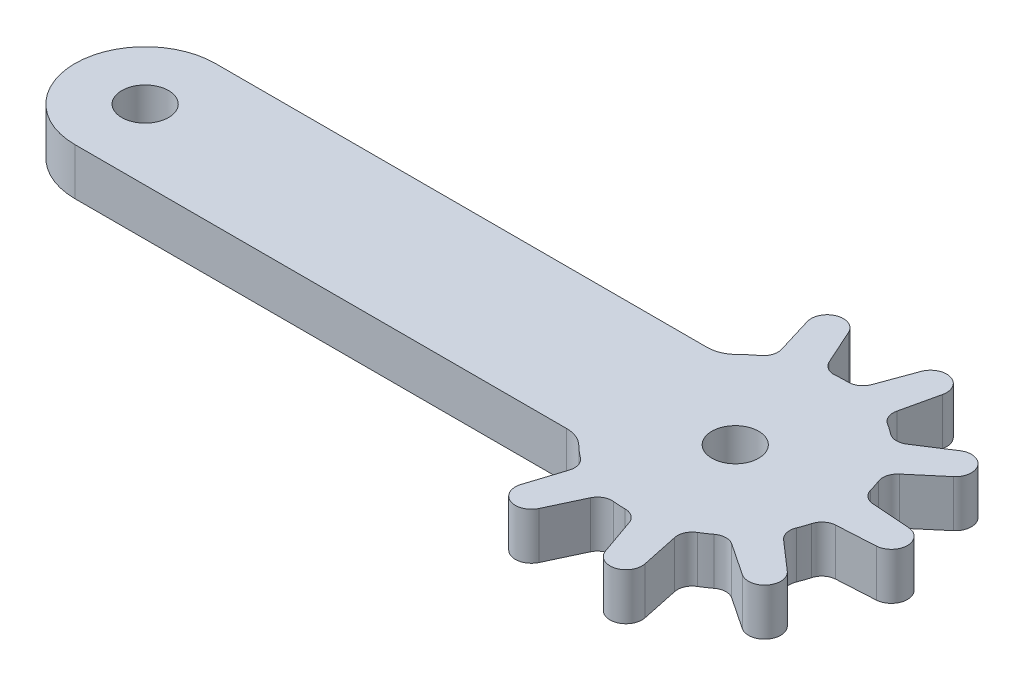
SolidWorks part; units mm, degrees
ref_plane "Alzado" through (0, 0, 0) normal (0, 0, 1) x (1, 0, 0)
ref_plane "Planta" through (0, 0, 0) normal (0, 1, 0) x (1, 0, 0)
ref_plane "Vista lateral" through (0, 0, 0) normal (1, 0, 0) x (0, 0, -1)
sketch "Croquis1" plane through (0, 0, 0) normal (0, 1, 0) x (1, 0, 0)
  line L1 (-20, 0) -> (20, 0)
  line L3 (-20, -9.525) -> (20, -9.525)
  arc A0 (-20, 0) -> (-20, -9.525) centre (-20, -4.7625) ccw
  arc A1 (20, -9.525) -> (20, 0) centre (20, -4.7625) ccw
  circle A2 centre (-20, -4.7625) radius 1.5875
  circle A3 centre (20, -4.7625) radius 1.5875
  dimension "D3" = 4.7625
  dimension "D5" = 3.175
  dimension "D6" = 3.175
  dimension "D1" = 40
  dimension "D2" = 9.525
  dimension "D4" = 40
extrude "Saliente-Extruir1" add sketch "Croquis1" along normal blind 3.175
sketch "Croquis2" plane through (0, 3.175, 0) normal (0, 1, 0) x (1, 0, 0)
  line L0 (20, -1004.7625) -> (20, 48995.2375) construction
  circle A0 centre (20, -4.7625) radius 7.5
  circle A1 centre (20, 14.7375) radius 9 construction
  circle A2 centre (20, -4.7625) radius 1.5875
  dimension "D1" = 15
  dimension "D2" = 18
  dimension "D3" = 19.5
extrude "Saliente-Extruir2" add sketch "Croquis2" against normal blind 3.175
sketch "Croquis8" plane through (0, 3.175, 0) normal (0, 1, 0) x (1, 0, 0)
  line L0 (20, -4.7625) -> (-13357.6554, 47973.2175) construction
  line L1 (20, -4.7625) -> (-13648.0155, 28548.14) construction
  line L2 (20, -4.7625) -> (-15507.6767, 26272.0183) construction
  line L3 (20, -4.7625) -> (-9125.193, 48956.5863) construction
  line L4 (20, -4.7625) -> (-38605.6068, 31745.2375) construction
  line L5 (14.9267, 5.8358) -> (16.1844, 1.6944)
  line L6 (16.8441, 6.5558) -> (18.6229, 2.61)
  arc A1 (18.6229, 2.61) -> (16.1844, 1.6944) centre (20, -4.7625) ccw
  arc A2 (16.8441, 6.5558) -> (14.9267, 5.8358) centre (20, -4.7625) ccw
  arc A3 (14.2062, -9.525) -> (14.2062, 0) centre (20, -4.7625) ccw construction
  dimension "D1" = 23.5
  dimension "D2" = 5
  dimension "D3" = 10
  dimension "D4" = 5
  dimension "D5" = 20
extrude "Saliente-Extruir3" add sketch "Croquis8" against normal blind 3.175
sketch "Croquis9" plane through (0, 3.175, 0) normal (0, 1, 0) x (1, 0, 0)
  line L0 (14.9267, 5.8358) -> (16.1844, 1.6944) construction
  line L1 (18.6229, 2.61) -> (16.8441, 6.5558) construction
  line L2 (14.9267, 5.8358) -> (15.2104, 4.9015)
  line L3 (17.2454, 5.6656) -> (16.8441, 6.5558)
  arc A0 (17.2454, 5.6656) -> (15.2104, 4.9015) centre (16.2525, 5.218) ccw
  arc A1 (16.8441, 6.5558) -> (14.9267, 5.8358) centre (20, -4.7625) ccw construction
  arc A2 (16.8441, 6.5558) -> (14.9267, 5.8358) centre (20, -4.7625) ccw
  line M3 (18.6229, 2.61) -> (16.8441, 6.5558)
  arc M4 (16.8441, 6.5558) -> (14.9267, 5.8358) centre (20, -4.7625) ccw
  line M5 (14.9267, 5.8358) -> (16.1844, 1.6944)
extrude "Cortar-Extruir1" cut sketch "Croquis9" against normal blind 10 contours A0 M3 M4 | A0 M4 M5
fillet "Redondeo3" radius 1 2 edges at (18.6229, 1.5875, -2.61) (16.1844, 1.5875, -1.6944)
pattern_circular "MatrizC2" count 7 every 37 about axis through (20, 0, 4.7625) along (0, 1, 0) of "Saliente-Extruir3", "Cortar-Extruir1", "Redondeo3"
fillet "Redondeo4" radius 2 2 edges at (14.2062, 1.5875, 9.525) (14.2062, 1.5875, 0)
